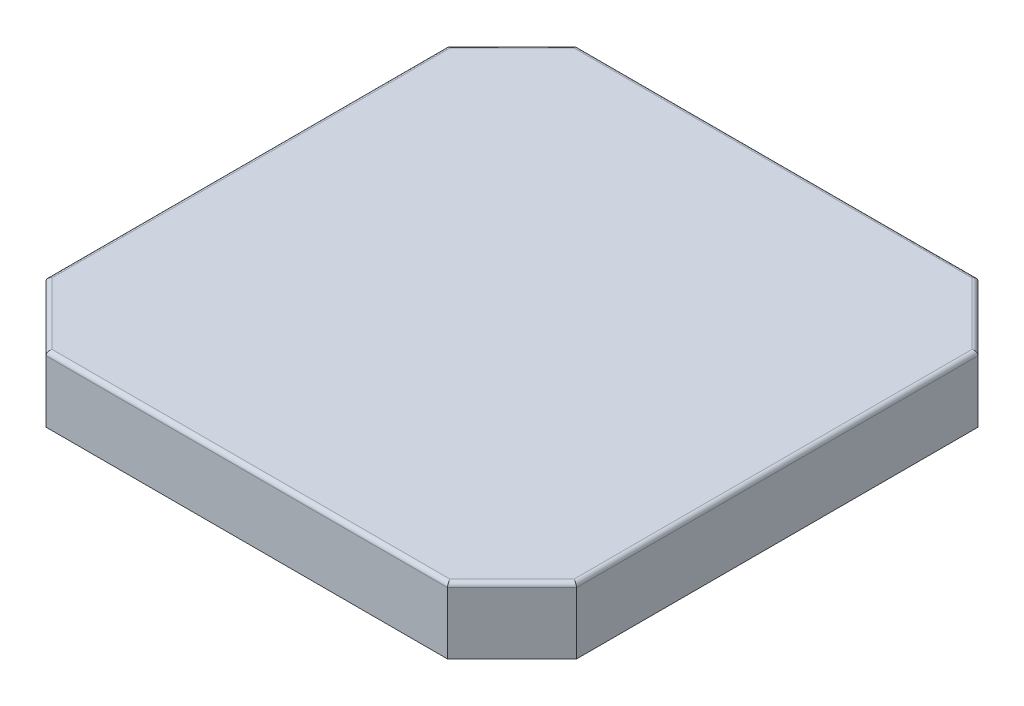
SolidWorks part; units mm, degrees
ref_plane "Plan de face" through (0, 0, 0) normal (0, 0, 1) x (1, 0, 0)
ref_plane "Plan de dessus" through (0, 0, 0) normal (0, 1, 0) x (1, 0, 0)
ref_plane "Plan de droite" through (0, 0, 0) normal (1, 0, 0) x (0, 0, -1)
sketch "Esquisse1" plane through (0, 0, 0) normal (0, 1, 0) x (1, 0, 0)
  line L1 (0, 0) -> (24.7, 0)
  line L2 (0, 0) -> (0, 24.7)
  line L3 (0, 24.7) -> (24.7, 24.7)
  line L4 (24.7, 0) -> (24.7, 24.7)
  dimension "D1" = 24.7
  dimension "D2" = 24.7
extrude "Boss.-Extru.1" add sketch "Esquisse1" along normal blind 3.08
chamfer "Chanfrein1" distance 3 angle 45 4 edges at (0, 1.54, -24.7) (24.7, 1.54, -24.7) (24.7, 1.54, 0) (0, 1.54, 0)
fillet "Congé1" radius 0.2 8 edges at (0, 3.08, -12.35) (1.5, 3.08, -1.5) (12.35, 3.08, 0) (23.2, 3.08, -1.5) (24.7, 3.08, -12.35) (23.2, 3.08, -23.2) (12.35, 3.08, -24.7) (1.5, 3.08, -23.2)
sketch "Esquisse2" plane through (0, 0, -24.7) normal (0, 0, -1) x (-1, 0, 0)
  line L0 (-21.7, 0) -> (-3, 0) construction
  line L1 (-15.35, 0) -> (-9.35, 0)
  line L2 (-15.35, 0) -> (-15.35, 2.88)
  line L3 (-15.35, 2.88) -> (-9.35, 2.88)
  line L4 (-9.35, 0) -> (-9.35, 2.88)
  line L5 (-3, 2.88) -> (-21.7, 2.88) construction
  line L6 (-21.7, 2.88) -> (-21.7, 0) construction
  line L7 (-3, 0) -> (-3, 2.88) construction
  point P8 (-21.7, 1.44)
  dimension "D1" = 6
  dimension "D2" = 6.35
  dimension "D3" = 6.35
extrude "Enlèv. mat.-Extru.1" cut sketch "Esquisse2" against normal blind 22.08
sketch "Esquisse3" plane through (0, 0, 0) normal (0, -1, 0) x (1, 0, 0)
  line L6 (3.1243, -24.4) -> (21.5757, -24.4)
  line L7 (24.4, -3.1243) -> (24.4, -21.5757)
  line L8 (3.1243, -0.3) -> (21.5757, -0.3)
  line L9 (0.3, -3.1243) -> (0.3, -21.5757)
  line L10 (3.1243, -0.3) -> (0.3, -3.1243)
  line L11 (3, 0) -> (0, -3) construction
  line L14 (24.4, -21.5757) -> (21.5757, -24.4)
  line L16 (3.1243, -24.4) -> (0.3, -21.5757)
  line L18 (21.7, -24.7) -> (24.7, -21.7) construction
  line L19 (0, -21.7) -> (3, -24.7) construction
  line L24 (21.5757, -0.3) -> (24.4, -3.1243)
  dimension "D2" = 0.3
  dimension "D4" = 0.3
  dimension "D5" = 0.3
extrude "Enlèv. mat.-Extru.2" cut sketch "Esquisse3" against normal up to surface (2.88 mm away) up to face at (12.35, 2.88, -13.66)
sketch "Sketch1" plane through (0, 0, -24.7) normal (0, 0, -1) x (-1, 0, 0)
  circle A0 centre (-11.4291, 1.4727) radius 0.5
  circle A1 centre (-13.0303, 1.4428) radius 0.5
  point P2 (-11.4291, 1.4727)
extrude "Boss-Extrude1" add sketch "Sketch1" along normal blind 0.5 separate body contours A1 | A0
